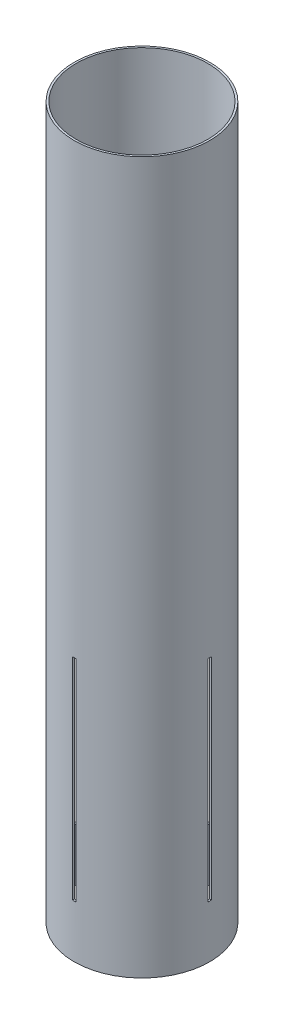
SolidWorks part; units mm, degrees
ref_plane "Front Plane" through (0, 0, 0) normal (0, 0, 1) x (1, 0, 0)
ref_plane "Top Plane" through (0, 0, 0) normal (0, 1, 0) x (1, 0, 0)
ref_plane "Right Plane" through (0, 0, 0) normal (1, 0, 0) x (0, 0, -1)
sketch "Sketch1" plane through (0, 0, 0) normal (0, 1, 0) x (1, 0, 0)
  circle A0 centre (0, 0) radius 65.405
  circle A1 centre (0, 0) radius 63.5
  dimension "D1" = 130.81
  dimension "D2" = 127
extrude "Boss-Extrude1" add sketch "Sketch1" along normal mid plane 685.8
sketch "Sketch4" plane through (0, 0, 0) normal (1, 0, 0) x (0, 0, -1)
  line L0 (0, -342.9) -> (0, 342.9)
  line L1 (-1.5875, -88.9) -> (1.5875, -88.9)
  line L2 (-1.5875, -88.9) -> (-1.5875, -292.1)
  line L3 (-1.5875, -292.1) -> (1.5875, -292.1)
  line L4 (1.5875, -88.9) -> (1.5875, -292.1)
  line L5 (-65.405, -342.9) -> (65.405, -342.9) construction
  line L6 (65.405, 342.9) -> (-65.405, 342.9) construction
  line L7 (-63.5, -342.9) -> (63.5, -342.9) construction
  line L8 (65.405, -342.9) -> (65.405, 342.9) construction
  dimension "D1" = 3.175
  dimension "D2" = 203.2
  dimension "D3" = 50.8
  dimension "D4" = 63.8175
extrude "Cut-Extrude2" cut sketch "Sketch4" along direction (1, 0, 0) on the side against the normal through all both and the other way through all contours L2 L3 L4 L1
pattern_circular "CirPattern4" count 2 every 90 about axis through (0, 342.9, 0) along (0, -1, 0) of "Cut-Extrude2"
equation "\"iDiameter\"= 5in"
equation "\"oDiameter\"= 5.15in"
equation "\"length\"= 26in"
